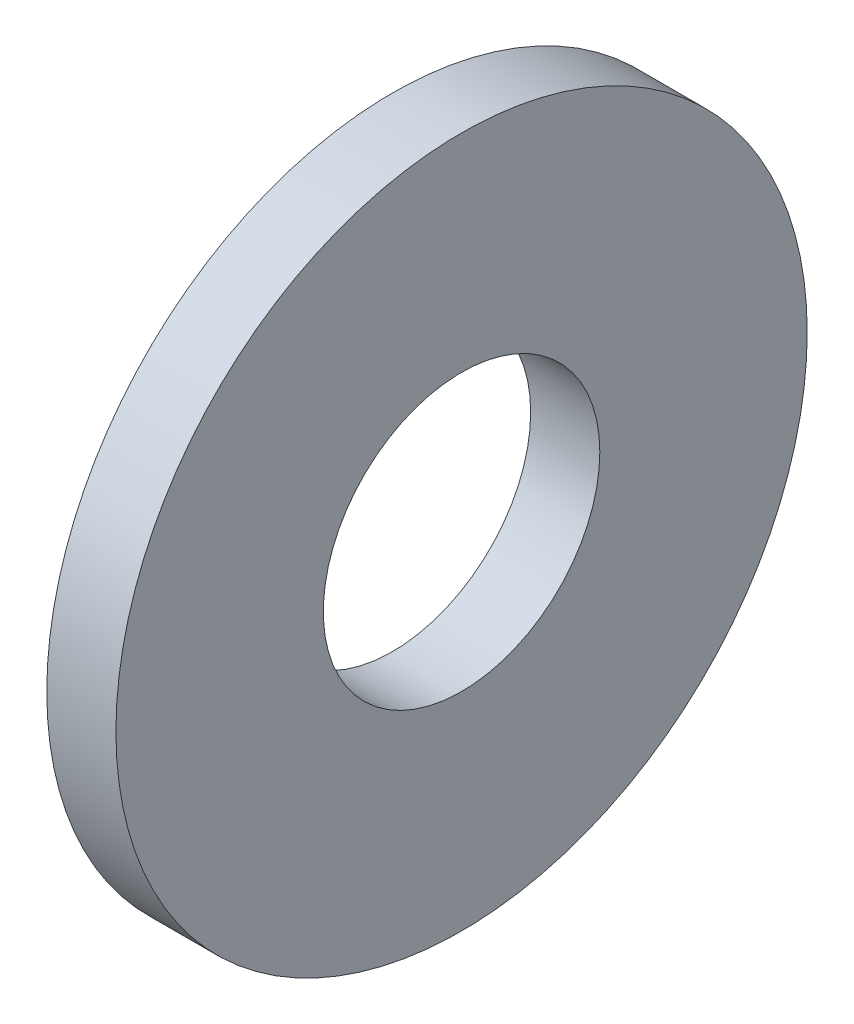
SolidWorks part; units mm, degrees
ref_plane "Plane1" through (0, 0, 0) normal (0, 0, 1) x (1, 0, 0)
ref_plane "Plane2" through (0, 0, 0) normal (0, 1, 0) x (1, 0, 0)
ref_plane "Plane3" through (0, 0, 0) normal (1, 0, 0) x (0, 0, -1)
other "Configuration Table"
sketch "Sketch1" plane through (0, 0, 0) normal (1, 0, 0) x (0, 0, -1)
  circle A0 centre (0, 0) radius 2
  circle A1 centre (0, 0) radius 5
  dimension "Insid_dia" = 4
  dimension "OutsideDia" = 10
extrude "Base-Extrude" add sketch "Sketch1" along normal blind 1
